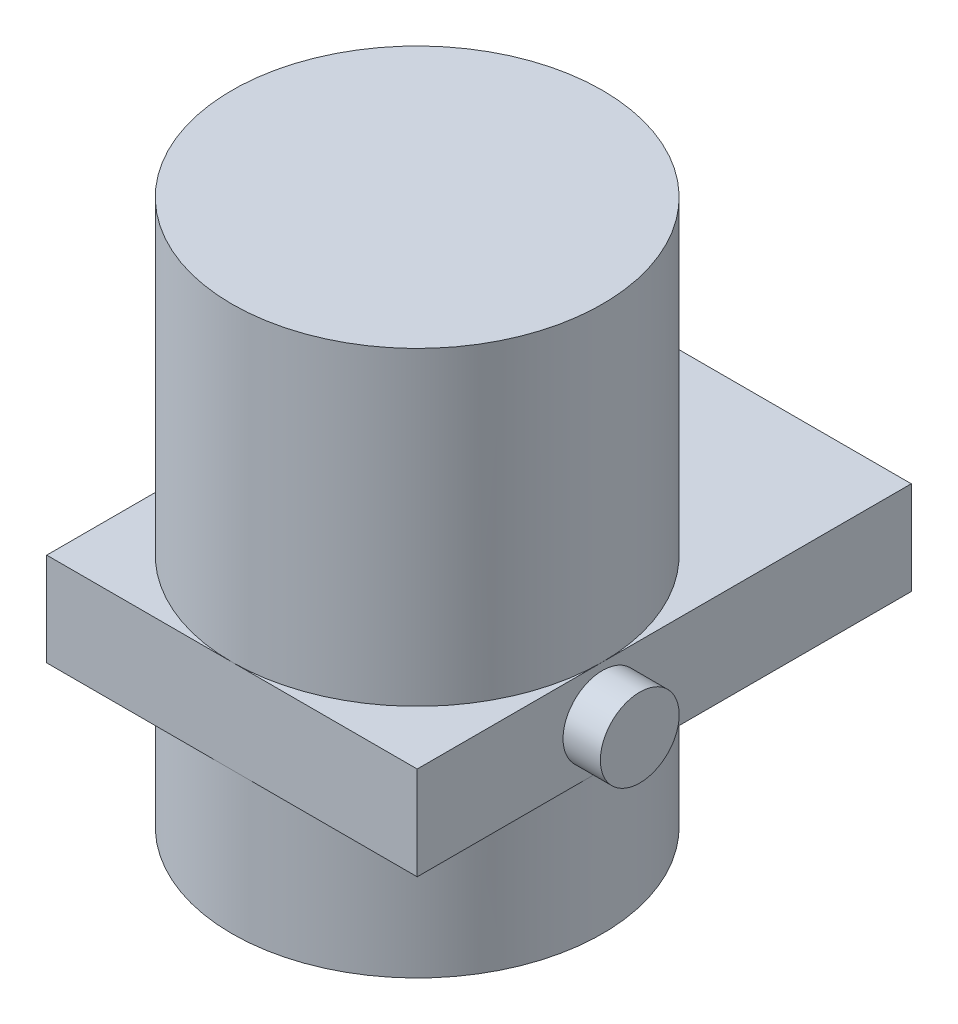
SolidWorks part; units mm, degrees
ref_plane "Front Plane" through (0, 0, 0) normal (0, 0, 1) x (1, 0, 0)
ref_plane "Top Plane" through (0, 0, 0) normal (0, 1, 0) x (1, 0, 0)
ref_plane "Right Plane" through (0, 0, 0) normal (1, 0, 0) x (0, 0, -1)
sketch "Sketch1" plane through (0, 0, 0) normal (0, 1, 0) x (1, 0, 0)
  line L1 (-125.984, -125.984) -> (125.984, -125.984)
  line L2 (-125.984, -125.984) -> (-125.984, 210.058)
  line L3 (-125.984, 210.058) -> (125.984, 210.058)
  line L4 (125.984, -125.984) -> (125.984, 210.058)
extrude "Boss-Extrude1" add sketch "Sketch1" along normal blind 63.5
sketch "Sketch2" plane through (0, 0, 0) normal (0, -1, 0) x (1, 0, 0)
  circle A0 centre (0, 0) radius 125.984
extrude "Boss-Extrude2" add sketch "Sketch2" along normal blind 96.52 and the other way blind 274.32
sketch "Sketch4" plane through (125.984, 0, 0) normal (1, 0, 0) x (0, 0, -1)
  circle A0 centre (0, 31.75) radius 26.797
extrude "Boss-Extrude7" add sketch "Sketch4" along normal blind 25.4
